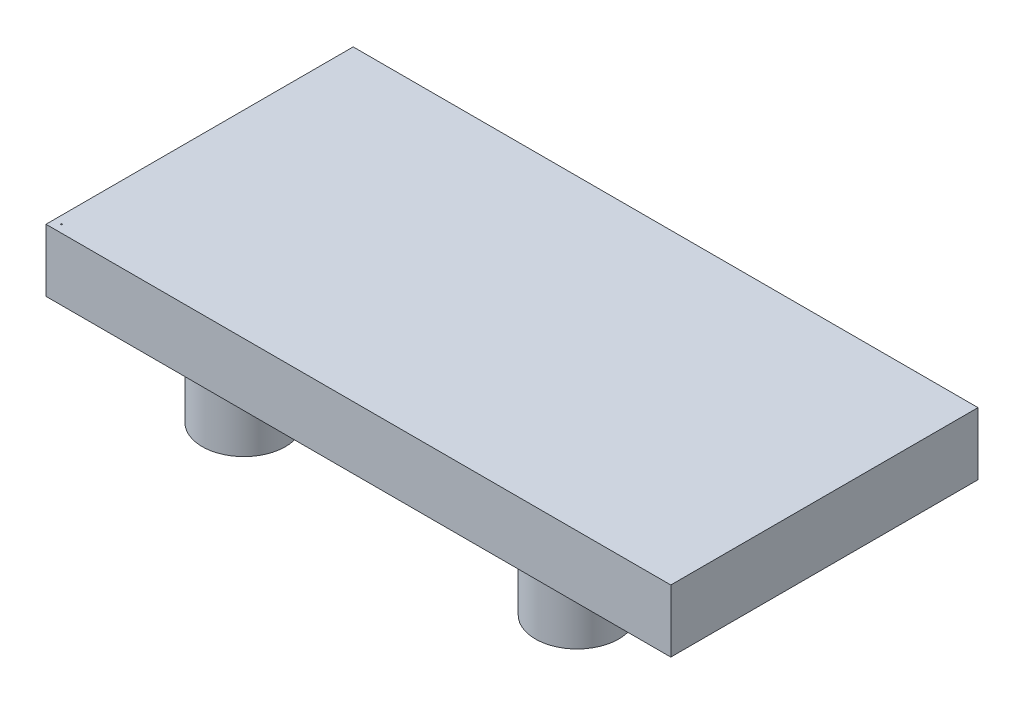
SolidWorks part; units mm, degrees
ref_plane "Front" through (0, 0, 0) normal (0, 0, 1) x (1, 0, 0)
ref_plane "Top" through (0, 0, 0) normal (0, 1, 0) x (1, 0, 0)
ref_plane "Right" through (0, 0, 0) normal (1, 0, 0) x (0, 0, -1)
sketch "Sketch1" plane through (0, 0, 0) normal (0, 1, 0) x (1, 0, 0)
  line L1 (0, 0) -> (3048, 0)
  line L2 (0, 0) -> (0, 1498.6)
  line L3 (0, 1498.6) -> (3048, 1498.6)
  line L4 (3048, 0) -> (3048, 1498.6)
  dimension "D1" = 3048
  dimension "D2" = 1498.6
extrude "Boss-Extrude1" add sketch "Sketch1" against normal blind 304.8
sketch "Sketch2" plane through (0, -304.8, 0) normal (0, -1, 0) x (1, 0, 0)
  circle A0 centre (711.2, -254) radius 203.2
  circle A1 centre (2336.8, -254) radius 203.2
  circle A2 centre (711.2, -1270) radius 203.2
  circle A3 centre (2336.8, -1270) radius 203.2
extrude "Boss-Extrude2" add sketch "Sketch2" along normal blind 304.8
sketch "Sketch3" plane through (0, 0, 0) normal (0, 1, 0) x (1, 0, 0)
  line L0 (0, 1498.6) -> (0, 0) construction
  line L1 (0, 0) -> (3048, 0) construction
  circle A0 centre (38.1, 38.1) radius 3.175
  dimension "D1" = 38.1
  dimension "D2" = 38.1
extrude "Cut-Extrude1" cut sketch "Sketch3" against normal blind 25.4
pattern_linear "LPattern1" [suppressed] count 57 spacing 25.4 count 118 spacing 25.4
